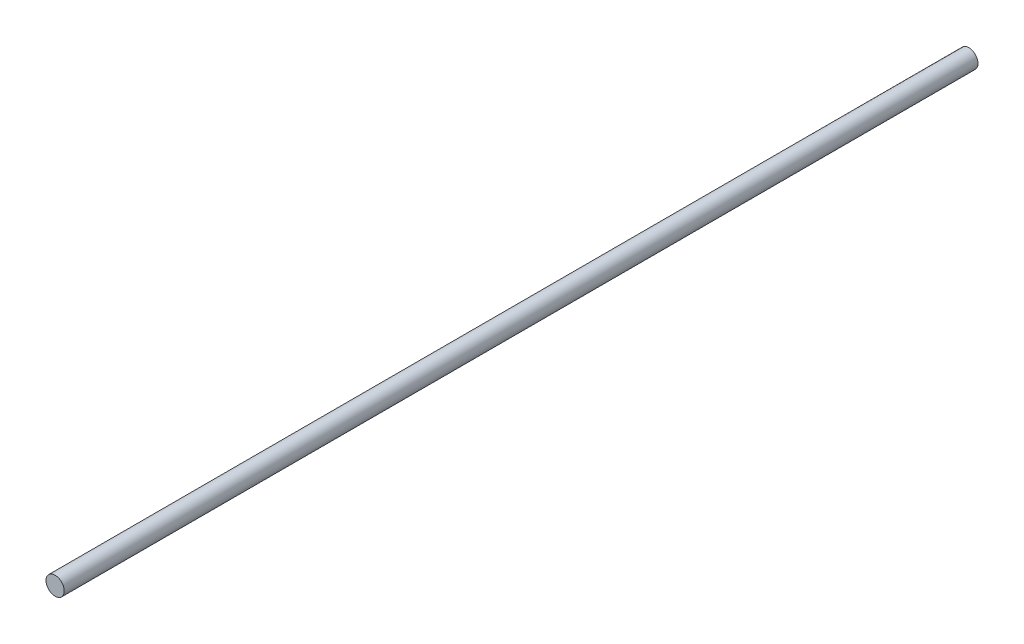
SolidWorks part; units mm, degrees
ref_plane "前视基准面" through (0, 0, 0) normal (0, 0, 1) x (1, 0, 0)
ref_plane "上视基准面" through (0, 0, 0) normal (0, 1, 0) x (1, 0, 0)
ref_plane "右视基准面" through (0, 0, 0) normal (1, 0, 0) x (0, 0, -1)
sketch "草图1" plane through (0, 0, 0) normal (0, 0, 1) x (1, 0, 0)
  circle A0 centre (0, 0) radius 5
  dimension "D1" = 10
extrude "凸台-拉伸1" add sketch "草图1" along normal blind 500
